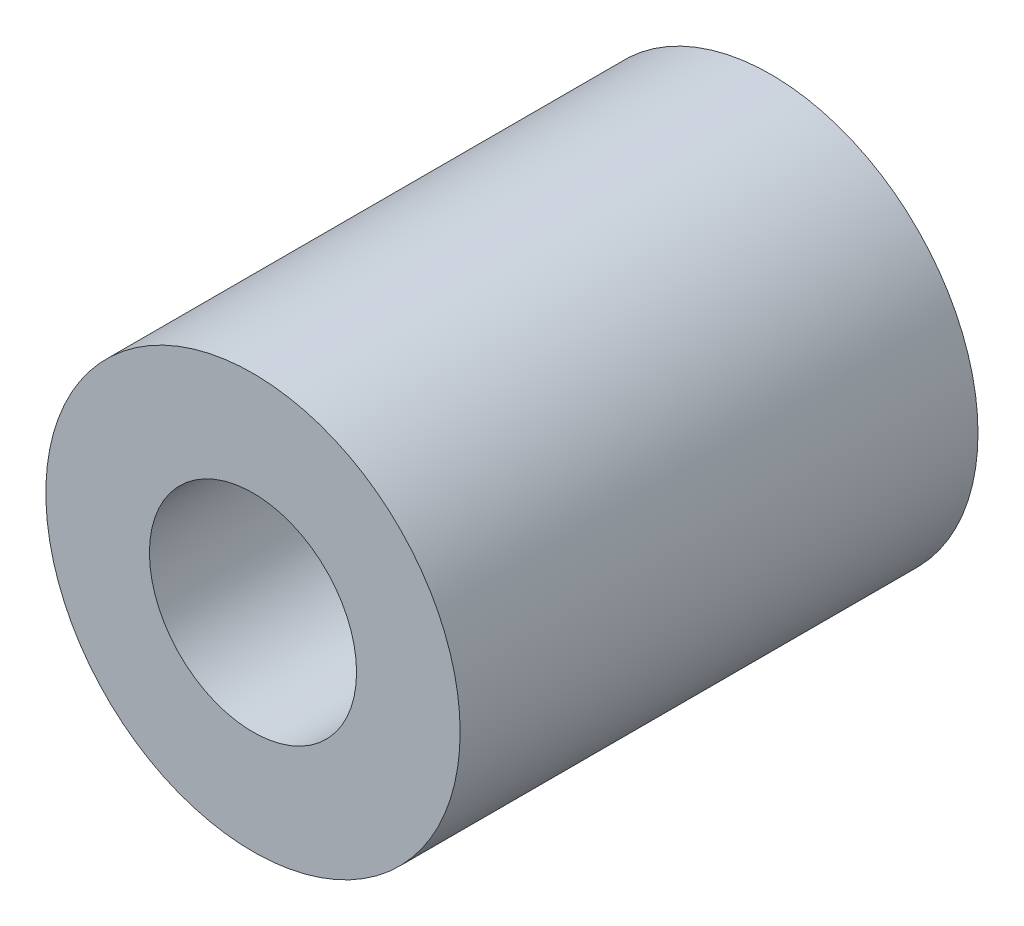
SolidWorks part; units mm, degrees
material "Alloy Steel (SS)"
ref_plane "Front Plane" through (0, 0, 0) normal (0, 0, 1) x (1, 0, 0)
ref_plane "Top Plane" through (0, 0, 0) normal (0, 1, 0) x (1, 0, 0)
ref_plane "Right Plane" through (0, 0, 0) normal (1, 0, 0) x (0, 0, -1)
sketch "Sketch2" plane through (0, 0, 0) normal (0, 0, 1) x (1, 0, 0)
  circle A0 centre (0, 0) radius 3
  circle A1 centre (0, 0) radius 6
  dimension "D1" = 6
  dimension "D2" = 12
extrude "Boss-Extrude1" add sketch "Sketch2" along normal blind 15
